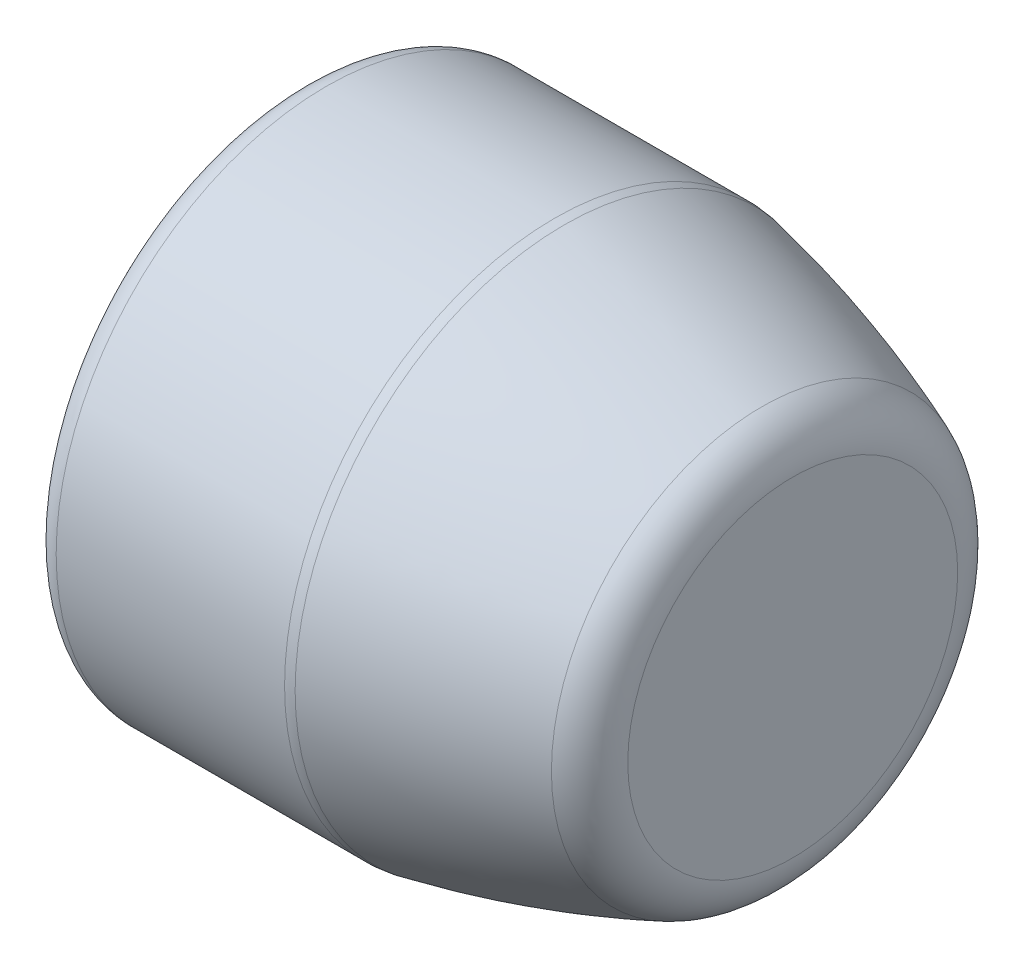
SolidWorks part; units mm, degrees
material "Tungsten"
ref_plane "Front Plane" through (0, 0, 0) normal (0, 0, 1) x (1, 0, 0)
ref_plane "Top Plane" through (0, 0, 0) normal (0, 1, 0) x (1, 0, 0)
ref_plane "Right Plane" through (0, 0, 0) normal (1, 0, 0) x (0, 0, -1)
sketch "Sketch1" plane through (0, 0, 0) normal (1, 0, 0) x (0, 0, -1)
  circle A0 centre (0, 0) radius 1.1
  dimension "D1" = 2.2
extrude "Boss-Extrude1" add sketch "Sketch1" along normal blind 2.5
fillet "Fillet1" radius 0.1 2 edges at (2.5, 0, -1.1) (0, 0, -1.1)
sketch "Sketch2" plane through (0, 0, 0) normal (0, 0, 1) x (1, 0, 0)
  line L0 (1.5498, 0) -> (2.5, 0)
  line L1 (2.5, -1) -> (2.5, 1) construction
  line L2 (1.5498, 1.1) -> (2.5, 1.1)
  line L3 (2.5, 1.1) -> (2.5, 0.8048)
  spline S0 degree 2 poles (1.5498, 1.1) (2.0489, 1.0025) (2.5, 0.8048) knots 0 0 0 0.445192 0.445192 0.445192
  dimension "D1" = 1.1
revolve "Cut-Revolve2" cut sketch "Sketch2" angle 360 about L0
fillet "Fillet2" radius 0.2 2 edges at (1.5498, 0, 1.1) (2.5, 0, 0.8048)
sketch "Sketch3" plane through (0, 0, 0) normal (0, 0, 1) x (1, 0, 0)
  line L0 (0, 0) -> (0, 1.1)
  line L1 (0, 1.1) -> (0.5, 1.1)
  line L2 (0.5, 1.1) -> (0.5, 0)
  line L3 (0.5, 0) -> (0, 0)
  dimension "D1" = 1.1
  dimension "D2" = 0.5
revolve "Cut-Revolve3" cut sketch "Sketch3" angle 360 about L3
fillet "Fillet3" radius 0.1 1 edges at (0.5, 0, -1.1)
